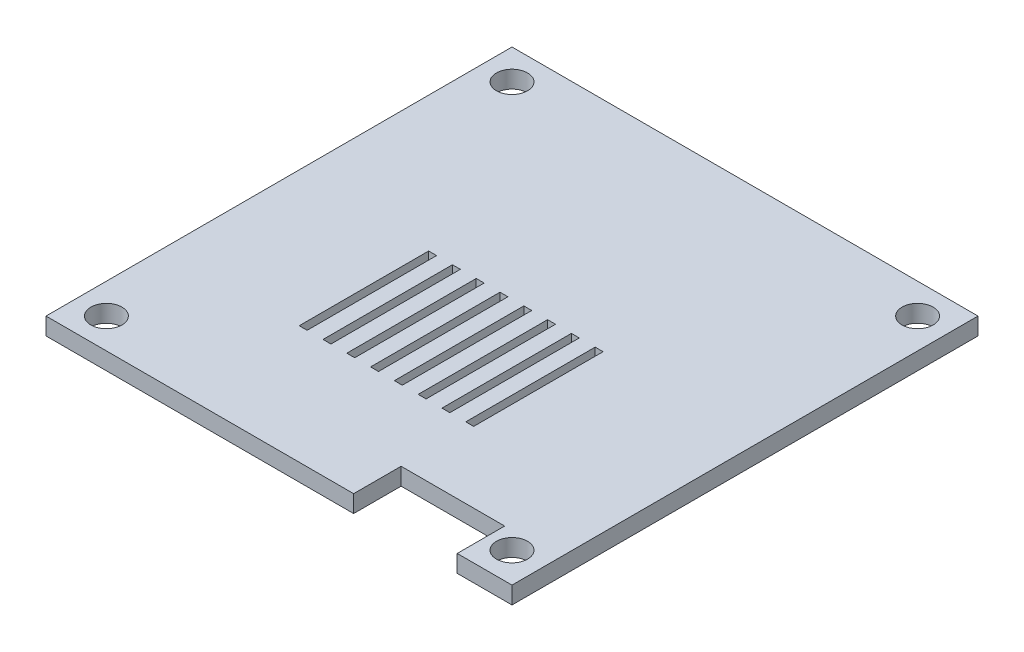
SolidWorks part; units mm, degrees
ref_plane "Front" through (0, 0, 0) normal (0, 0, 1) x (1, 0, 0)
ref_plane "Top" through (0, 0, 0) normal (0, 1, 0) x (1, 0, 0)
ref_plane "Right" through (0, 0, 0) normal (1, 0, 0) x (0, 0, -1)
sketch "草图3" plane through (0, 0, 0) normal (0, 1, 0) x (1, 0, 0)
  line L0 (16.9, -20) -> (20, -20)
  line L1 (-20, -20) -> (12.4, -20)
  line L2 (20, -20) -> (20, 20)
  line L3 (-27, 27) -> (-27, -27)
  line L4 (-27, -27) -> (27, -27)
  line L5 (27, -27) -> (27, 27)
  line L6 (27, 27) -> (-27, 27)
  line L7 (-8.6, 1.7) -> (-7.6812, 1.7)
  line L8 (-5.8437, 1.7) -> (-4.925, 1.7)
  line L9 (20.65, -20) -> (20, -20)
  line L10 (16.9, -6) -> (12.4, -6)
  line L11 (12.4, -6) -> (12.4, -19.5)
  line L12 (-10.4, 20) -> (-4.1, 20)
  line L13 (16.9, -6) -> (16.9, -19.5)
  line L14 (-20, 20) -> (-20, -20)
  line L15 (-3.0875, 1.7) -> (-2.1687, 1.7)
  line L16 (-0.3312, 1.7) -> (0.5875, 1.7)
  line L17 (2.425, 1.7) -> (3.3438, 1.7)
  line L18 (5.1813, 1.7) -> (6.1, 1.7)
  line L19 (8.8563, -13.3) -> (7.9375, -13.3)
  line L20 (8.65, -20) -> (8.65, -27)
  line L21 (-8.6, 1.7) -> (-8.6, -13.3)
  line L22 (-7.6812, -13.3) -> (-8.6, -13.3)
  line L23 (-8.6, -13.3) -> (-8.6029, -13.3589)
  line L24 (-10.4375, -13.3) -> (-11.3562, -13.3)
  line L25 (-10.4375, 1.7) -> (-11.3562, 1.7)
  line L26 (6.1, 1.7) -> (6.1, -13.3)
  line L27 (-4.925, -13.3) -> (-4.925, 1.7)
  line L28 (-11.3562, -13.3) -> (-11.3562, 1.7)
  line L29 (-3.0875, -13.3) -> (-3.0875, 1.7)
  line L30 (-10.4375, -13.3) -> (-10.4375, 1.7)
  line L31 (-2.1687, -13.3) -> (-2.1687, 1.7)
  line L32 (8.8563, 1.7) -> (7.9375, 1.7)
  line L33 (-5.8437, -13.3) -> (-5.8437, 1.7)
  line L34 (8.8563, -13.3) -> (8.8563, 1.7)
  line L35 (-7.6812, -13.3) -> (-7.6812, 1.7)
  line L36 (-0.3312, -13.3) -> (-0.3312, 1.7)
  line L37 (0.5875, -13.3) -> (0.5875, 1.7)
  line L38 (5.1813, -13.3) -> (6.1, -13.3)
  line L39 (2.425, -13.3) -> (2.425, 1.7)
  line L40 (3.3438, -13.3) -> (3.3438, 1.7)
  line L41 (2.425, -13.3) -> (3.3438, -13.3)
  line L42 (5.1813, -13.3) -> (5.1813, 1.7)
  line L43 (-0.3312, -13.3) -> (0.5875, -13.3)
  line L44 (-3.0875, -13.3) -> (-2.1687, -13.3)
  line L45 (-5.8437, -13.3) -> (-4.925, -13.3)
  line L46 (7.9375, -13.3) -> (7.9375, 1.7)
  line L47 (20.65, -20) -> (20.65, -27)
  line L48 (12.4, -19.5) -> (12.4, -20)
  line L49 (16.9, -19.5) -> (16.9, -20)
  line L50 (-20, -20) -> (20, -20) construction
  line L51 (-20, 20) -> (20, 20)
  line L52 (-16.7, 20) -> (-10.4, 20)
  line L53 (20, 20) -> (-20, 20) construction
  line L54 (12.4, -20) -> (16.9, -20)
  line L56 (8.65, -21.5) -> (20.65, -21.5)
  circle A0 centre (-23.5, -23.5) radius 1.8
  circle A1 centre (23.5, -23.5) radius 1.8
  circle A2 centre (-23.5, 23.5) radius 1.8
  circle A3 centre (23.5, 23.5) radius 1.8
  point P0 (0, 0)
  point P61 (-10.8969, 1.7)
  dimension "D1" = 7
extrude "凸台-拉伸2" add sketch "草图3" along normal blind 2
